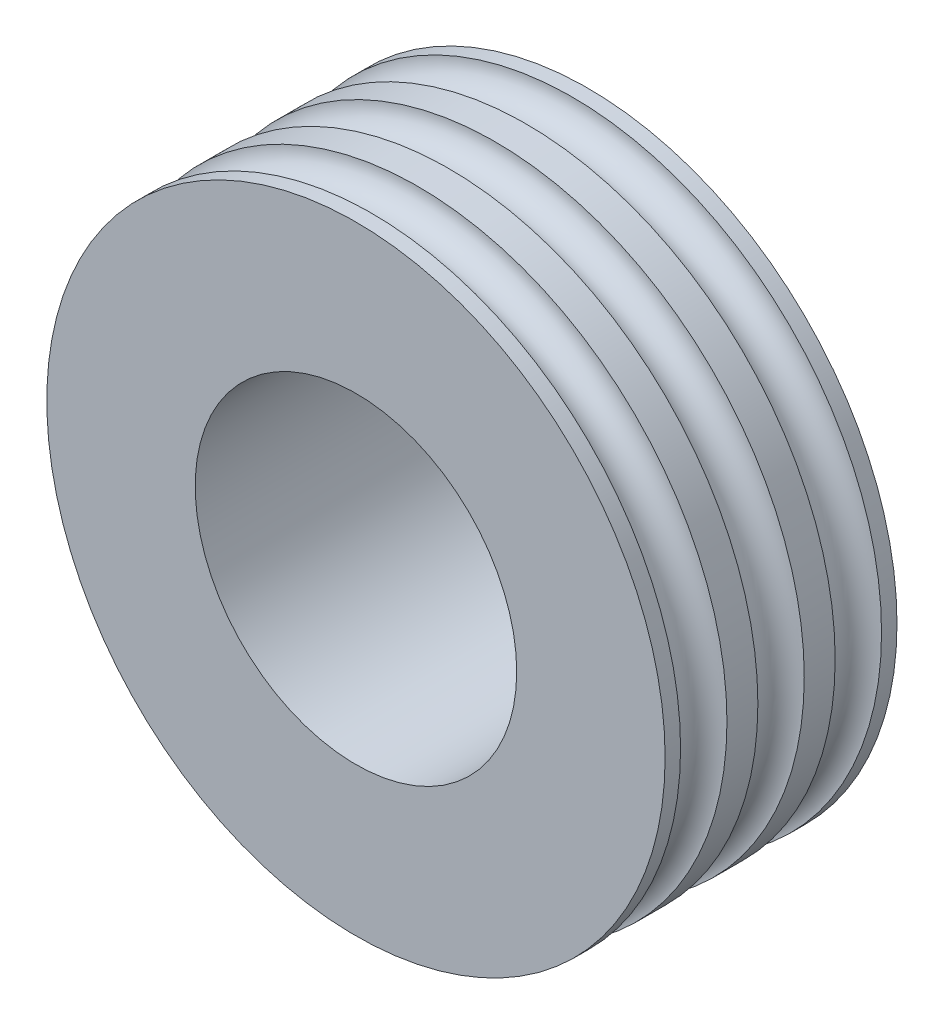
SolidWorks part; units mm, degrees
ref_plane "Front Plane" through (0, 0, 0) normal (0, 0, 1) x (1, 0, 0)
ref_plane "Top Plane" through (0, 0, 0) normal (0, 1, 0) x (1, 0, 0)
ref_plane "Right Plane" through (0, 0, 0) normal (1, 0, 0) x (0, 0, -1)
sketch "Sketch2" plane through (0, 0, 0) normal (1, 0, 0) x (0, 0, -1)
  line L0 (0.25, 2.6) -> (0.25, 5)
  line L1 (0.25, 5) -> (0, 5)
  line L2 (-1, 5) -> (-1, 2.6)
  line L4 (-1, 2.6) -> (0.25, 2.6)
  line L5 (-3.0147, 0) -> (3.0268, 0) construction
  line L6 (-0.75, 5) -> (-1, 5)
  arc A0 (-0.75, 5) -> (0, 5) centre (-0.375, 5) ccw
  dimension "D2" = 1.25
  dimension "D4" = 0.25
  dimension "D5" = 0.25
revolve "Revolve1" add sketch "Sketch2" angle 360 about L5
ref_plane "Plane1" through (0, 0, -0.25) normal (0, 0, -1) x (-1, 0, 0)
mirror "Mirror1" about plane through (0, 0, -0.25) normal (0, 0, -1) of bodies 101
mirror "Mirror2" about plane through (0, 5, 1) normal (0, 0, -1) of "Revolve1"
